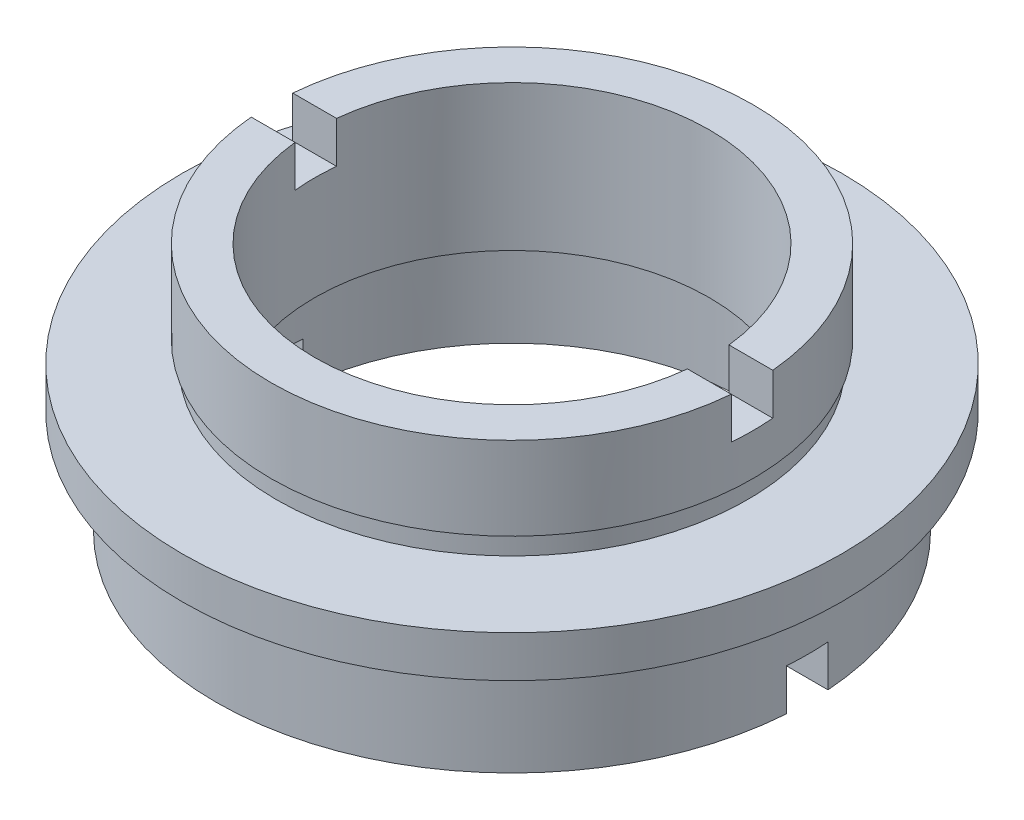
SolidWorks part; units mm, degrees
ref_plane "前视基准面" through (0, 0, 0) normal (0, 0, 1) x (1, 0, 0)
ref_plane "上视基准面" through (0, 0, 0) normal (0, 1, 0) x (1, 0, 0)
ref_plane "右视基准面" through (0, 0, 0) normal (1, 0, 0) x (0, 0, -1)
sketch "草图1" plane through (0, 0, 0) normal (0, 0, 1) x (1, 0, 0)
  line L0 (0, 22.6775) -> (0, 0) construction
  line L1 (-9.5, 12) -> (-11.6, 12)
  line L2 (-11.6, 12) -> (-11.6, 8)
  line L3 (-11.6, 8) -> (-11.35, 8)
  line L4 (-11.35, 8) -> (-11.35, 7)
  line L5 (-11.35, 7) -> (-15.875, 7)
  line L6 (-15.875, 7) -> (-15.875, 5)
  line L7 (-15.875, 5) -> (-13.75, 5)
  line L8 (-13.75, 5) -> (-13.75, 4)
  line L9 (-13.75, 4) -> (-14.25, 4)
  line L10 (-14.25, 4) -> (-14.25, 0)
  line L11 (-14.25, 0) -> (-11.1, 0)
  line L12 (-11.1, 0) -> (-11.1, 4)
  line L13 (-9.5, 5) -> (-11.7, 5)
  line L14 (-11.7, 5) -> (-11.7, 4)
  line L15 (-11.7, 4) -> (-11.1, 4)
  line L16 (-9.5, 12) -> (-9.5, 5)
  point P3 (-11.4, 4)
  point P5 (-15.875, 6)
  dimension "D2" = 1
  dimension "D3" = 1
  dimension "D4" = 5
  dimension "D5" = 5
  dimension "D6" = 11.6
  dimension "D7" = 15.875
  dimension "D8" = 14.25
  dimension "D9" = 13.75
  dimension "D10" = 11.35
  dimension "D11" = 11.1
  dimension "D12" = 0
  dimension "D13" = 11.7
  dimension "D14" = 9.5
  dimension "D15" = 12
  dimension "D16" = 7
  dimension "D17" = 1
revolve "旋转1" add sketch "草图1" angle 360 about L0
cosmetic thread "装饰螺纹线1" parameters "D2"=22.2
cosmetic thread "装饰螺纹线2" parameters "D2"=27.5
cosmetic thread "装饰螺纹线3" parameters "D2"=23.2
cosmetic thread "装饰螺纹线4" parameters "D2"=20
sketch "草图2" plane through (0, 0, 0) normal (1, 0, 0) x (0, 0, -1)
  line L0 (11.1, 12) -> (-11.1, 12) construction
  line L1 (-1, 13.594) -> (1, 13.594)
  line L2 (-1, 13.594) -> (-1, 10)
  line L3 (-1, 10) -> (1, 10)
  line L4 (1, 13.594) -> (1, 10)
  line L5 (-1, 2) -> (1, 2)
  line L6 (-1, 2) -> (-1, -4.6679)
  line L7 (-1, -4.6679) -> (1, -4.6679)
  line L8 (1, 2) -> (1, -4.6679)
  dimension "D1" = 2
  dimension "D2" = 1
  dimension "D3" = 2
  dimension "D4" = 1
  dimension "D5" = 2
  dimension "D6" = 2
extrude "切除-拉伸1" cut sketch "草图2" against normal mid plane 79
